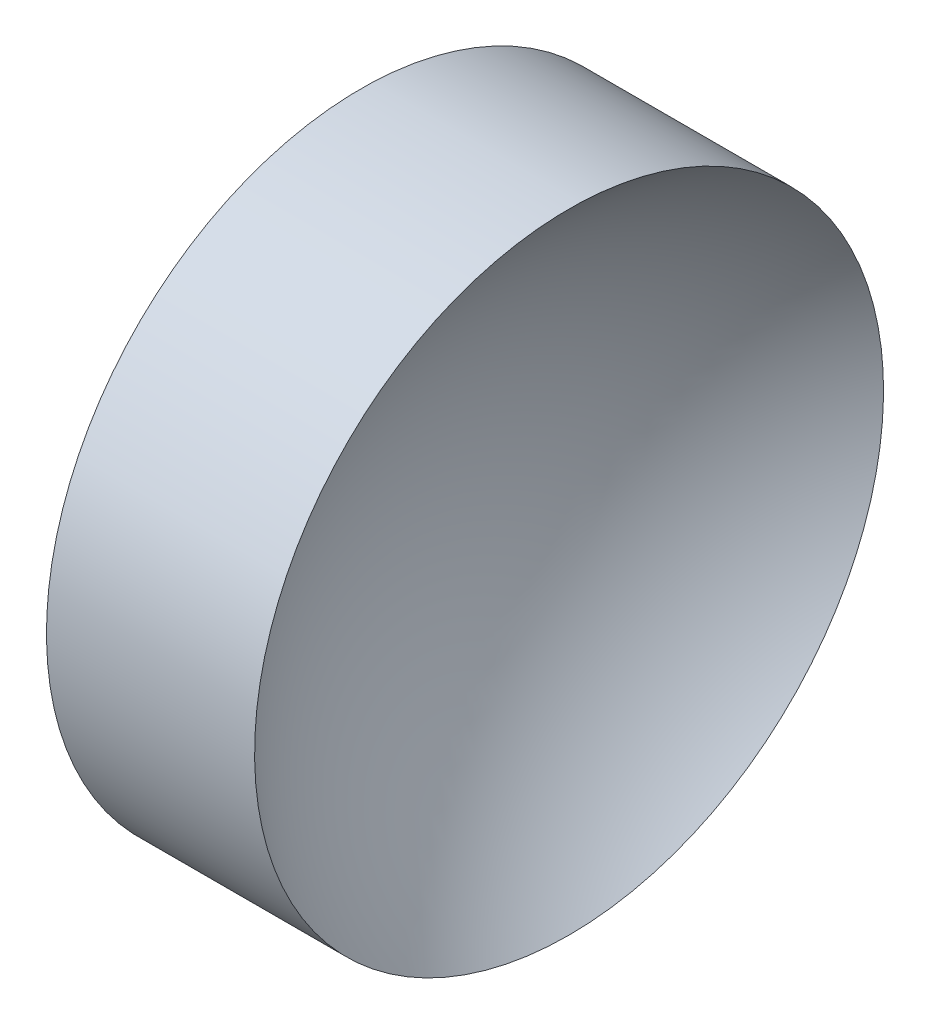
SolidWorks part; units mm, degrees
ref_plane "前视基准面" through (0, 0, 0) normal (0, 0, 1) x (1, 0, 0)
ref_plane "上视基准面" through (0, 0, 0) normal (0, 1, 0) x (1, 0, 0)
ref_plane "右视基准面" through (0, 0, 0) normal (1, 0, 0) x (0, 0, -1)
sketch "草图1" plane through (0, 0, 0) normal (0, 0, 1) x (1, 0, 0)
  line L0 (43.012, 26.0623) -> (53.9941, 26.0623) construction
  line L1 (44.8544, 26.0623) -> (44.8544, 34.0623)
  line L2 (44.8544, 34.0623) -> (50.1492, 34.0623)
  line L3 (46.3544, 26.0623) -> (44.8544, 26.0623)
  arc A0 (50.1492, 34.0623) -> (46.3544, 26.0623) centre (56.6844, 26.0623) ccw
revolve "旋转1" add sketch "草图1" angle 360 about L0
